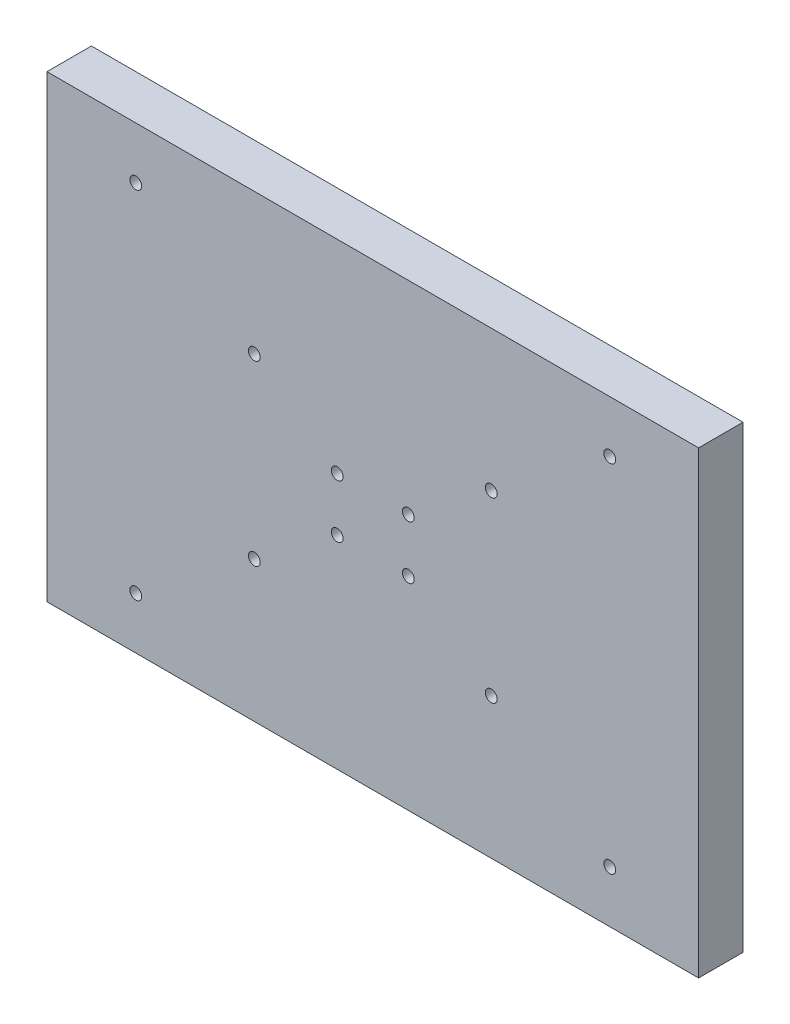
SolidWorks part; units mm, degrees
material "Balsa"
ref_plane "Front Plane" through (0, 0, 0) normal (0, 0, 1) x (1, 0, 0)
ref_plane "Top Plane" through (0, 0, 0) normal (0, 1, 0) x (1, 0, 0)
ref_plane "Right Plane" through (0, 0, 0) normal (1, 0, 0) x (0, 0, -1)
sketch "Sketch1" plane through (0, 0, 0) normal (0, 0, 1) x (1, 0, 0)
  line L0 (-327.7517, -129.8772) -> (-327.7517, 25.1228) construction
  line L2 (-437.7517, -129.8772) -> (-217.7517, -129.8772)
  line L3 (-437.7517, -129.8772) -> (-437.7517, 25.1228)
  line L4 (-437.7517, 25.1228) -> (-217.7517, 25.1228)
  line L5 (-217.7517, -129.8772) -> (-217.7517, 25.1228)
  line L20 (-437.7517, -52.3772) -> (-217.7517, -52.3772) construction
  line L21 (-339.7517, -43.3772) -> (-339.7517, -61.3772) construction
  circle A0 centre (-315.7517, -61.3772) radius 2
  circle A1 centre (-339.7517, -61.3772) radius 2
  circle A2 centre (-315.7517, -43.3772) radius 2
  circle A3 centre (-339.7517, -43.3772) radius 2
  circle A4 centre (-247.7517, -112.3772) radius 2
  circle A5 centre (-407.7517, -112.3772) radius 2
  circle A6 centre (-247.7517, 7.6228) radius 2
  circle A7 centre (-407.7517, 7.6228) radius 2
  circle A8 centre (-287.7517, -82.3772) radius 2
  circle A9 centre (-367.7517, -82.3772) radius 2
  circle A10 centre (-287.7517, -22.3772) radius 2
  circle A11 centre (-367.7517, -22.3772) radius 2
  point P25 (-339.7517, -52.3772)
  dimension "D9" = 4
  dimension "D3" = 120
  dimension "D5" = 60
  dimension "D1" = 220
  dimension "D2" = 155
  dimension "D4" = 160
  dimension "D6" = 80
  dimension "D10" = 24
  dimension "D11" = 18
  dimension "D12" = 98
extrude "Boss-Extrude1" add sketch "Sketch1" along normal blind 15
